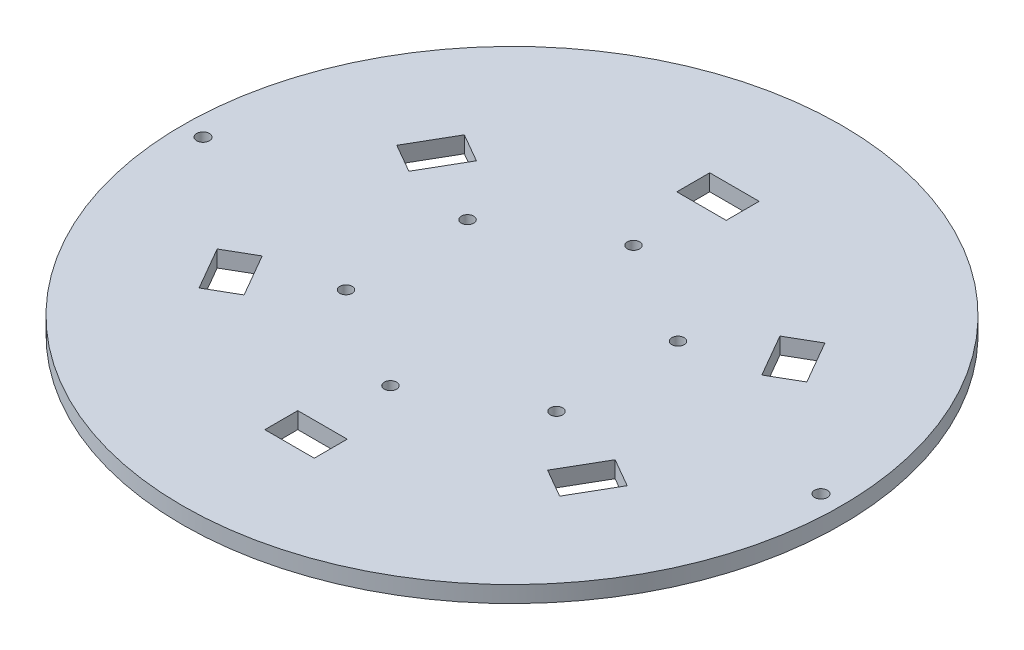
SolidWorks part; units mm, degrees
ref_plane "Front Plane" through (0, 0, 0) normal (0, 0, 1) x (1, 0, 0)
ref_plane "Top Plane" through (0, 0, 0) normal (0, 1, 0) x (1, 0, 0)
ref_plane "Right Plane" through (0, 0, 0) normal (1, 0, 0) x (0, 0, -1)
sketch "Sketch1" plane through (0, 0, 0) normal (0, 1, 0) x (1, 0, 0)
  arc A0 (-6, 79.7747) -> (6, 79.7747) centre (0, 0) ccw
  arc A1 (-6, 79.7747) -> (6, 79.7747) centre (0, 0) cw
  dimension "D1" = 160
extrude "Boss-Extrude1" add sketch "Sketch1" along normal mid plane 4
sketch "Sketch2" plane through (0, -2, 0) normal (0, -1, 0) x (1, 0, 0)
  circle A0 centre (75, 0) radius 1.55
  circle A1 centre (-75, 0) radius 1.55
  dimension "D1" = 3.1
  dimension "D2" = 75
  dimension "D3" = 3.1
  dimension "D4" = 75
extrude "Cut-Extrude1" cut sketch "Sketch2" against normal through all
sketch "Sketch3" plane through (0, 2, 0) normal (0, 1, 0) x (1, 0, 0)
  line L0 (43.7654, 32.1962) -> (49.7654, 21.8038)
  line L1 (-6, 54) -> (6, 54)
  line L2 (-6, 54) -> (-6, 46)
  line L3 (-6, 46) -> (6, 46)
  line L4 (6, 54) -> (6, 46)
  line L5 (-6, 54) -> (6, 46) construction
  line L6 (-6, 46) -> (6, 54) construction
  line L7 (43.7654, 32.1962) -> (36.8372, 28.1962)
  line L8 (36.8372, 28.1962) -> (42.8372, 17.8038)
  line L9 (49.7654, 21.8038) -> (42.8372, 17.8038)
  line L10 (43.7654, 32.1962) -> (42.8372, 17.8038) construction
  line L11 (36.8372, 28.1962) -> (49.7654, 21.8038) construction
  line L12 (49.7654, -21.8038) -> (43.7654, -32.1962)
  line L13 (49.7654, -21.8038) -> (42.8372, -17.8038)
  line L14 (42.8372, -17.8038) -> (36.8372, -28.1962)
  line L15 (43.7654, -32.1962) -> (36.8372, -28.1962)
  line L16 (49.7654, -21.8038) -> (36.8372, -28.1962) construction
  line L17 (42.8372, -17.8038) -> (43.7654, -32.1962) construction
  line L18 (6, -54) -> (-6, -54)
  line L19 (6, -54) -> (6, -46)
  line L20 (6, -46) -> (-6, -46)
  line L21 (-6, -54) -> (-6, -46)
  line L22 (6, -54) -> (-6, -46) construction
  line L23 (6, -46) -> (-6, -54) construction
  line L24 (-43.7654, -32.1962) -> (-49.7654, -21.8038)
  line L25 (-43.7654, -32.1962) -> (-36.8372, -28.1962)
  line L26 (-36.8372, -28.1962) -> (-42.8372, -17.8038)
  line L27 (-49.7654, -21.8038) -> (-42.8372, -17.8038)
  line L28 (-43.7654, -32.1962) -> (-42.8372, -17.8038) construction
  line L29 (-36.8372, -28.1962) -> (-49.7654, -21.8038) construction
  line L30 (-49.7654, 21.8038) -> (-43.7654, 32.1962)
  line L31 (-49.7654, 21.8038) -> (-42.8372, 17.8038)
  line L32 (-42.8372, 17.8038) -> (-36.8372, 28.1962)
  line L33 (-43.7654, 32.1962) -> (-36.8372, 28.1962)
  line L34 (-49.7654, 21.8038) -> (-36.8372, 28.1962) construction
  line L35 (-42.8372, 17.8038) -> (-43.7654, 32.1962) construction
  circle A0 centre (0, 0) radius 70 construction
  point P3 (0, 50)
  point P11 (43.3013, 25)
  point P16 (43.3013, -25)
  point P21 (0, -50)
  point P26 (-43.3013, -25)
  point P31 (-43.3013, 25)
  dimension "D1" = 140
  dimension "D2" = 12
  dimension "D3" = 8
  dimension "D4" = 50
  dimension "D6" = 50
  dimension "D7" = 50
  dimension "D5" = 6
extrude "Cut-Extrude2" cut sketch "Sketch3" against normal through all
sketch "Sketch4" plane through (0, 2, 0) normal (0, 1, 0) x (1, 0, 0)
  circle A0 centre (-25.5477, -14.75) radius 1.5 construction
  circle A1 centre (-25.5477, -14.75) radius 1.5
  circle A2 centre (-25.5477, -14.75) radius 1.5
  circle A3 centre (-25.5477, 14.75) radius 1.5 construction
  circle A4 centre (-25.5477, 14.75) radius 1.5
  circle A5 centre (-25.5477, -14.75) radius 1.5 construction
  circle A6 centre (-25.5477, -14.75) radius 1.5
  circle A7 centre (-25.5477, -14.75) radius 1.5
  circle A8 centre (0, 29.5) radius 1.5 construction
  circle A9 centre (0, 29.5) radius 1.5
  circle A10 centre (25.5477, 14.75) radius 1.5 construction
  circle A11 centre (25.5477, 14.75) radius 1.5
  circle A12 centre (25.5477, -14.75) radius 1.5 construction
  circle A13 centre (25.5477, -14.75) radius 1.5
  circle A14 centre (0, -29.5) radius 1.5 construction
  circle A15 centre (0, -29.5) radius 1.5
extrude "Cut-Extrude4" cut sketch "Sketch4" against normal blind 10 contours A15 | A4 | A1 | A13 | A11 | A9
